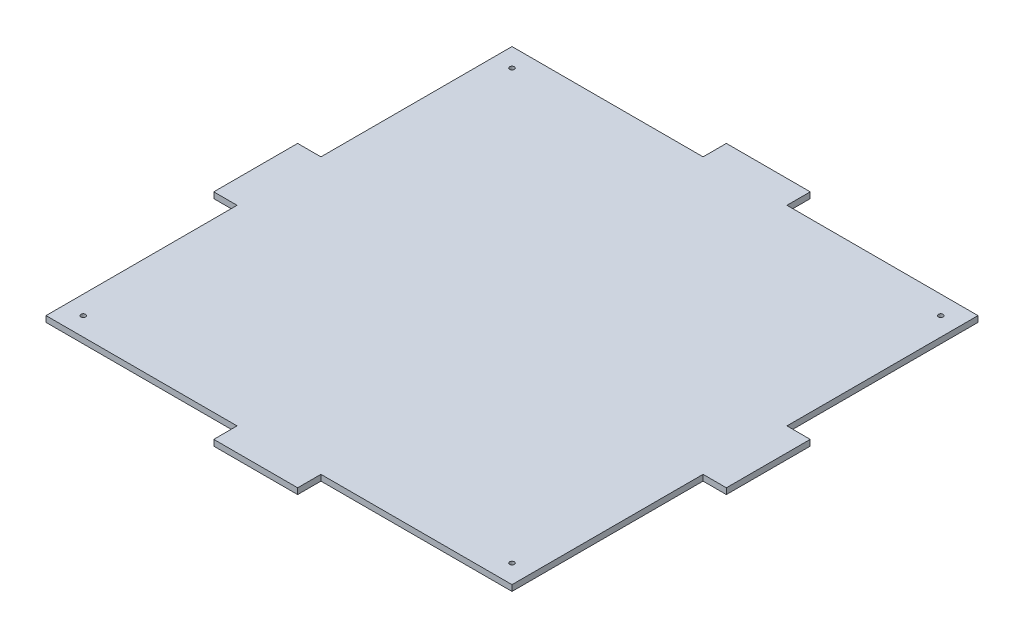
SolidWorks part; units mm, degrees
ref_plane "Front Plane" through (0, 0, 0) normal (0, 0, 1) x (1, 0, 0)
ref_plane "Top Plane" through (0, 0, 0) normal (0, 1, 0) x (1, 0, 0)
ref_plane "Right Plane" through (0, 0, 0) normal (1, 0, 0) x (0, 0, -1)
sketch "Sketch2" plane through (0, 0, 0) normal (0, 1, 0) x (1, 0, 0)
  line L1 (-125, -125) -> (125, -125)
  line L2 (-125, -125) -> (-125, 125)
  line L3 (-125, 125) -> (125, 125)
  line L4 (125, -125) -> (125, 125)
  line L5 (-125, -125) -> (125, 125) construction
  line L6 (-125, 125) -> (125, -125) construction
  point P0 (0, 0)
  dimension "250" = 250
extrude "Base" add sketch "Sketch2" along normal blind 3.175
sketch "Sketch3" plane through (0, 3.175, 0) normal (0, 1, 0) x (1, 0, 0)
  line L0 (-125, 0) -> (125, 0) construction
  line L1 (-125, 125) -> (-125, -125) construction
  line L2 (125, -125) -> (125, 125) construction
  line L3 (-43.75, 125) -> (-43.75, -125) construction
  line L4 (125, 125) -> (-125, 125) construction
  line L5 (-125, -125) -> (125, -125) construction
  line L6 (0, 125) -> (0, -125) construction
  line L11 (-48.05, 28) -> (-39.45, 28)
  line L12 (-48.05, 28) -> (-48.05, 43.35)
  line L13 (-48.05, 43.35) -> (-39.45, 43.35)
  line L14 (-39.45, 28) -> (-39.45, 43.35)
  line L15 (-48.05, 28) -> (-39.45, 43.35) construction
  line L16 (-48.05, 43.35) -> (-39.45, 28) construction
  line L21 (-48.05, -43.35) -> (-39.45, -43.35)
  line L22 (-48.05, -43.35) -> (-48.05, -28)
  line L23 (-48.05, -28) -> (-39.45, -28)
  line L24 (-39.45, -43.35) -> (-39.45, -28)
  line L25 (-48.05, -43.35) -> (-39.45, -28) construction
  line L26 (-48.05, -28) -> (-39.45, -43.35) construction
  line L27 (48.05, -28) -> (39.45, -28)
  line L28 (39.45, -43.35) -> (39.45, -28)
  line L29 (48.05, -43.35) -> (39.45, -43.35)
  line L30 (48.05, -43.35) -> (48.05, -28)
  line L31 (48.05, 43.35) -> (39.45, 43.35)
  line L32 (39.45, 28) -> (39.45, 43.35)
  line L33 (48.05, 28) -> (39.45, 28)
  line L34 (48.05, 28) -> (48.05, 43.35)
  point P12 (-43.75, 35.675)
  point P17 (-43.75, -35.675)
  dimension "D1" = 43.75
  dimension "D2" = 8.6
  dimension "D3" = 15.35
  dimension "D4" = 56
  dimension "D5" = 28
sketch "Sketch10" plane through (0, 0, -125) normal (0, 0, -1) x (-1, 0, 0)
  line L0 (-125, 1.5875) -> (125, 1.5875) construction
  line L1 (-125, 3.175) -> (-125, 0) construction
  line L2 (125, 3.175) -> (125, 0) construction
  line L8 (-125, 3.175) -> (125, 3.175) construction
  line L9 (-22.5, 0) -> (22.5, 0)
  line L10 (-22.5, 0) -> (-22.5, 3.175)
  line L11 (-22.5, 3.175) -> (22.5, 3.175)
  line L12 (22.5, 0) -> (22.5, 3.175)
  line L13 (-22.5, 0) -> (22.5, 3.175) construction
  line L14 (-22.5, 3.175) -> (22.5, 0) construction
  point P6 (0, 1.5875)
  dimension "D1" = 45
extrude "Jigsaw1" add sketch "Sketch10" along normal blind 12.5
sketch "Sketch11" plane through (-125, 0, 0) normal (-1, 0, 0) x (0, 0, 1)
  line L0 (-125, 1.5875) -> (125, 1.5875) construction
  line L1 (-125, 3.175) -> (-125, 0) construction
  line L2 (125, 3.175) -> (125, 0) construction
  line L9 (-22.5, 0) -> (22.5, 0)
  line L10 (-22.5, 0) -> (-22.5, 3.175)
  line L11 (-22.5, 3.175) -> (22.5, 3.175)
  line L12 (22.5, 0) -> (22.5, 3.175)
  line L13 (-22.5, 0) -> (22.5, 3.175) construction
  line L14 (-22.5, 3.175) -> (22.5, 0) construction
  point P6 (0, 1.5875)
  dimension "D1" = 45
  dimension "D2" = 3.175
extrude "Jigsaw2" add sketch "Sketch11" along normal blind 12.5
sketch "Sketch13" plane through (0, 0, 125) normal (0, 0, 1) x (1, 0, 0)
  line L0 (-125, 1.5875) -> (125, 1.5875) construction
  line L3 (-125, 0) -> (-125, 3.175) construction
  line L9 (-22.5, 0) -> (22.5, 0)
  line L10 (-22.5, 0) -> (-22.5, 3.175)
  line L11 (-22.5, 3.175) -> (22.5, 3.175)
  line L12 (22.5, 0) -> (22.5, 3.175)
  line L13 (-22.5, 0) -> (22.5, 3.175) construction
  line L14 (-22.5, 3.175) -> (22.5, 0) construction
  line L15 (125, 3.175) -> (125, 0) construction
  point P6 (0, 1.5875)
  dimension "D1" = 45
  dimension "D2" = 3.175
extrude "Jigsaw3" add sketch "Sketch13" along normal blind 12.5
sketch "Sketch14" plane through (125, 0, 0) normal (1, 0, 0) x (0, 0, -1)
  line L0 (-125, 1.5875) -> (125, 1.5875) construction
  line L3 (-125, 3.175) -> (-125, 0) construction
  line L9 (-22.5, 0) -> (22.5, 0)
  line L10 (-22.5, 0) -> (-22.5, 3.175)
  line L11 (-22.5, 3.175) -> (22.5, 3.175)
  line L12 (22.5, 0) -> (22.5, 3.175)
  line L13 (-22.5, 0) -> (22.5, 3.175) construction
  line L14 (-22.5, 3.175) -> (22.5, 0) construction
  line L15 (125, 3.175) -> (125, 0) construction
  point P6 (0, 1.5875)
  dimension "D1" = 45
  dimension "D2" = 3.175
extrude "Jigsaw4" add sketch "Sketch14" along normal blind 12.5
hole_wizard "Standoff Holes" positions "3DSketch4" profile "Sketch20" tap size "M3" standard "ISO" end condition through all
sketch3d "3DSketch4"
  line L0 (-22.5, 3.175, -125) -> (-125, 3.175, -125) construction
  line L1 (-125, 3.175, -125) -> (-125, 3.175, -22.5) construction
  point P0 (-115, 3.175, -115)
  dimension "D1" = 10
  dimension "D2" = 10
sketch "Sketch20" plane through (-115, 3.175, -115) normal (1, 0, 0) x (0, 0, 1)
  line L0 (0, 0) -> (0, 3.175)
  line L1 (0, 3.175) -> (1.25, 3.175)
  line L2 (1.25, 3.175) -> (1.25, 0)
  line L5 (1.25, 0) -> (0, 0)
  line L11 (0, -6.35) -> (0, 107.95) construction
  dimension "Thru Tap Drill Dia." = 2.5
  dimension "Thru Tap Drill Depth" = 3.175
cosmetic thread "Hole Thread1" parameters "D2"=3
sketch "Sketch21" plane through (0, 3.175, 0) normal (0, 1, 0) x (1, 0, 0)
  line L0 (0, -137.5) -> (0, 137.5)
  line L1 (22.5, -137.5) -> (-22.5, -137.5) construction
  line L2 (-22.5, 137.5) -> (22.5, 137.5) construction
  line L3 (-137.5, 0) -> (137.5, 0)
  line L4 (-137.5, -22.5) -> (-137.5, 22.5) construction
  line L5 (137.5, 22.5) -> (137.5, -22.5) construction
  circle A0 centre (-115, 115) radius 1.25
  circle A1 centre (115, 115) radius 1.25
  circle A2 centre (115, -115) radius 1.25
  circle A3 centre (-115, -115) radius 1.25
extrude "Standoff Holes 2" cut sketch "Sketch21" against normal blind 10 contours A1 | A2 | A3
